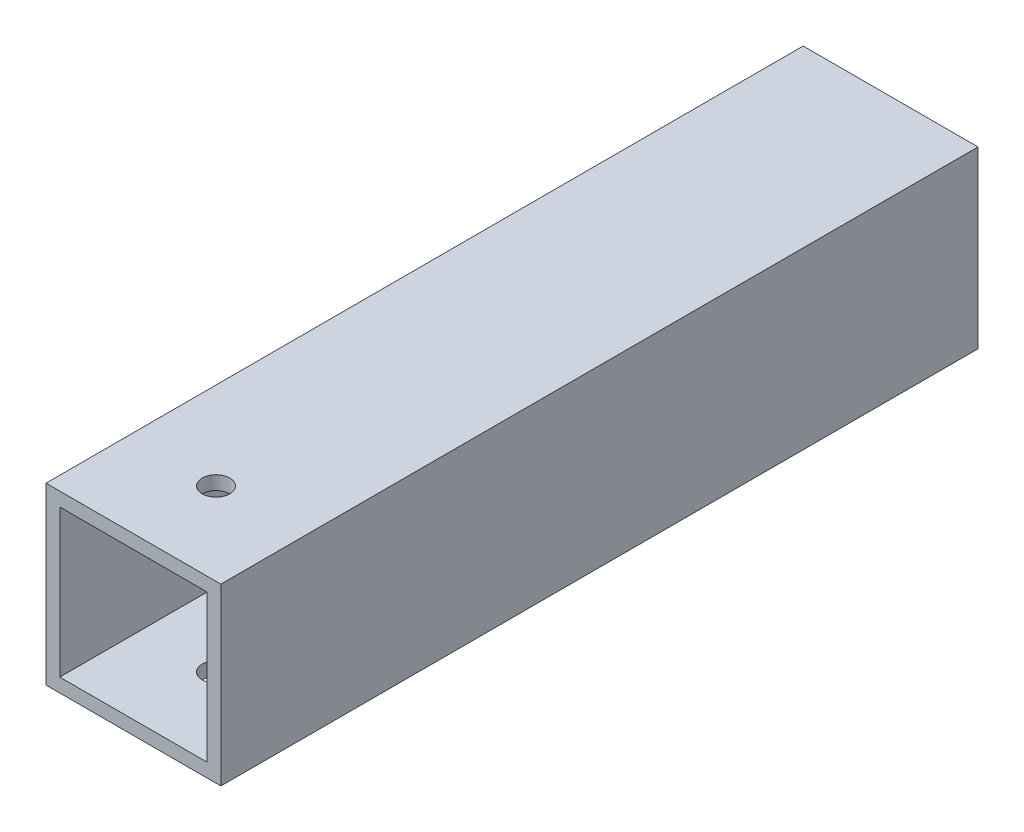
SolidWorks part; units mm, degrees
material "AISI 1020"
ref_plane "Front Plane" through (0, 0, 0) normal (0, 0, 1) x (1, 0, 0)
ref_plane "Top Plane" through (0, 0, 0) normal (0, 1, 0) x (1, 0, 0)
ref_plane "Right Plane" through (0, 0, 0) normal (1, 0, 0) x (0, 0, -1)
sketch "Sketch1" plane through (0, 0, 0) normal (0, 0, 1) x (1, 0, 0)
  line L1 (0, 0) -> (25.4, 0)
  line L2 (0, 0) -> (0, 25.4)
  line L3 (0, 25.4) -> (25.4, 25.4)
  line L4 (25.4, 0) -> (25.4, 25.4)
  line L5 (2, 23.4) -> (23.4, 23.4)
  line L6 (2, 23.4) -> (2, 2)
  line L7 (2, 2) -> (23.4, 2)
  line L8 (23.4, 23.4) -> (23.4, 2)
  dimension "D1" = 2
  dimension "D2" = 2
  dimension "D3" = 25.4
  dimension "D4" = 2
extrude "Boss-Extrude1" add sketch "Sketch1" along normal blind 110
sketch "Sketch2" plane through (0, 0, 0) normal (0, -1, 0) x (1, 0, 0)
  line L0 (0, 110) -> (25.4, 110) construction
  circle A0 centre (12.7, 98) radius 2
  dimension "D1" = 4
  dimension "D2" = 12
extrude "Cut-Extrude1" cut sketch "Sketch2" against normal through all contours A0
